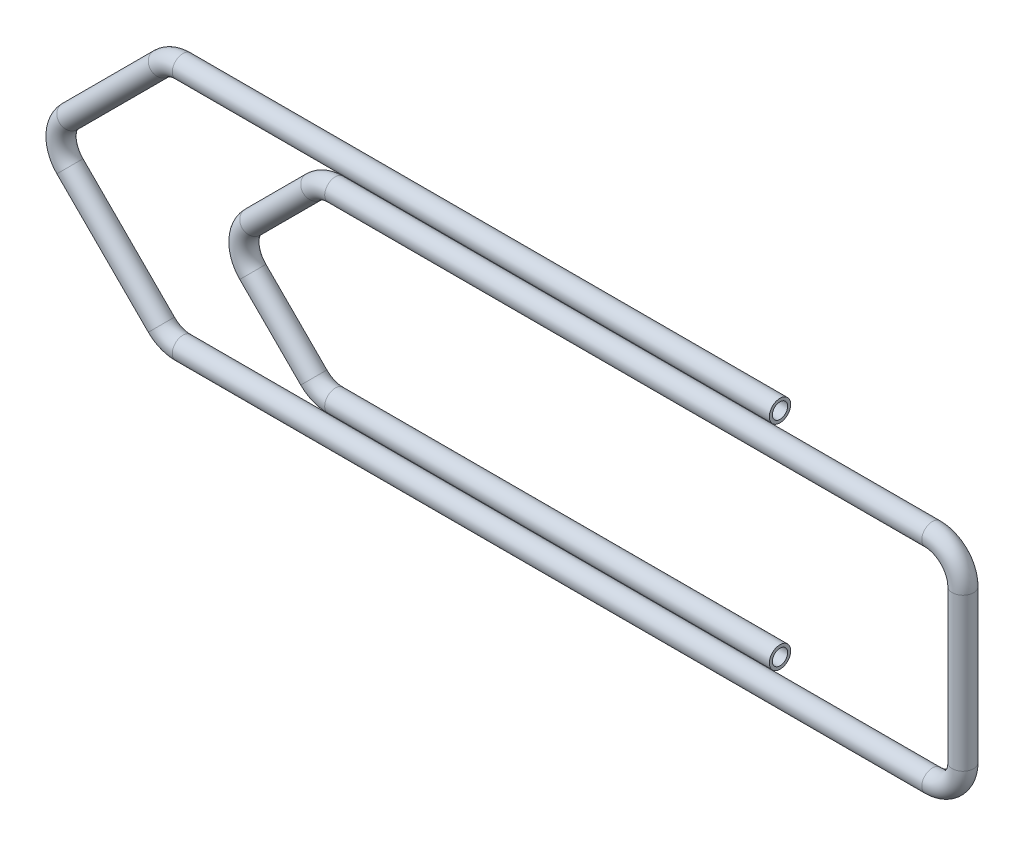
SolidWorks part; units mm, degrees
material "Obyčejná uhlíková ocel"
ref_plane "Přední rovina" through (0, 0, 0) normal (0, 0, 1) x (1, 0, 0)
ref_plane "Horní rovina" through (0, 0, 0) normal (0, 1, 0) x (1, 0, 0)
ref_plane "Pravá rovina" through (0, 0, 0) normal (1, 0, 0) x (0, 0, -1)
sketch "Skica1" plane through (0, 0, 0) normal (0, 0, 1) x (1, 0, 0)
  line L0 (0, 0) -> (-19.5858, 0)
  line L1 (-20.2929, -0.2929) -> (-23.2929, -3.2929)
  line L2 (-19.5858, -8) -> (5, -8)
  line L3 (6, -7) -> (6, -2)
  line L4 (5, -1) -> (-14.5858, -1)
  line L5 (-15.2929, -1.2929) -> (-17.2929, -3.2929)
  line L6 (-14.5858, -7) -> (0, -7)
  line L7 (-23.2929, -4.7071) -> (-20.2929, -7.7071)
  line L8 (-17.2929, -4.7071) -> (-15.2929, -6.7071)
  arc A0 (5, -8) -> (6, -7) centre (5, -7) ccw
  arc A1 (6, -2) -> (5, -1) centre (5, -2) ccw
  arc A2 (-15.2929, -6.7071) -> (-14.5858, -7) centre (-14.5858, -6) ccw
  arc A3 (-14.5858, -1) -> (-15.2929, -1.2929) centre (-14.5858, -2) ccw
  arc A4 (-17.2929, -3.2929) -> (-17.2929, -4.7071) centre (-16.5858, -4) ccw
  arc A5 (-20.2929, -7.7071) -> (-19.5858, -8) centre (-19.5858, -7) ccw
  arc A6 (-19.5858, 0) -> (-20.2929, -0.2929) centre (-19.5858, -1) ccw
  arc A7 (-23.2929, -3.2929) -> (-23.2929, -4.7071) centre (-22.5858, -4) ccw
  point P27 (-15, -7)
  point P30 (-15, -1)
  point P33 (-18, -4)
  point P36 (-20, -8)
  point P39 (-20, 0)
  point P42 (-24, -4)
  dimension "D6" = 1
  dimension "D1" = 30
  dimension "D2" = 20
  dimension "D3" = 15
  dimension "D4" = 8
  dimension "D5" = 1
sketch "Skica2" plane through (0, 0, 0) normal (1, 0, 0) x (0, 0, -1)
  circle A0 centre (0, 0) radius 0.35
  dimension "D1" = 0.7
sweep "Táhnout po křivce1" add profiles "Skica2" path "Skica1"
shell "Skořepina1" thickness 0.1
